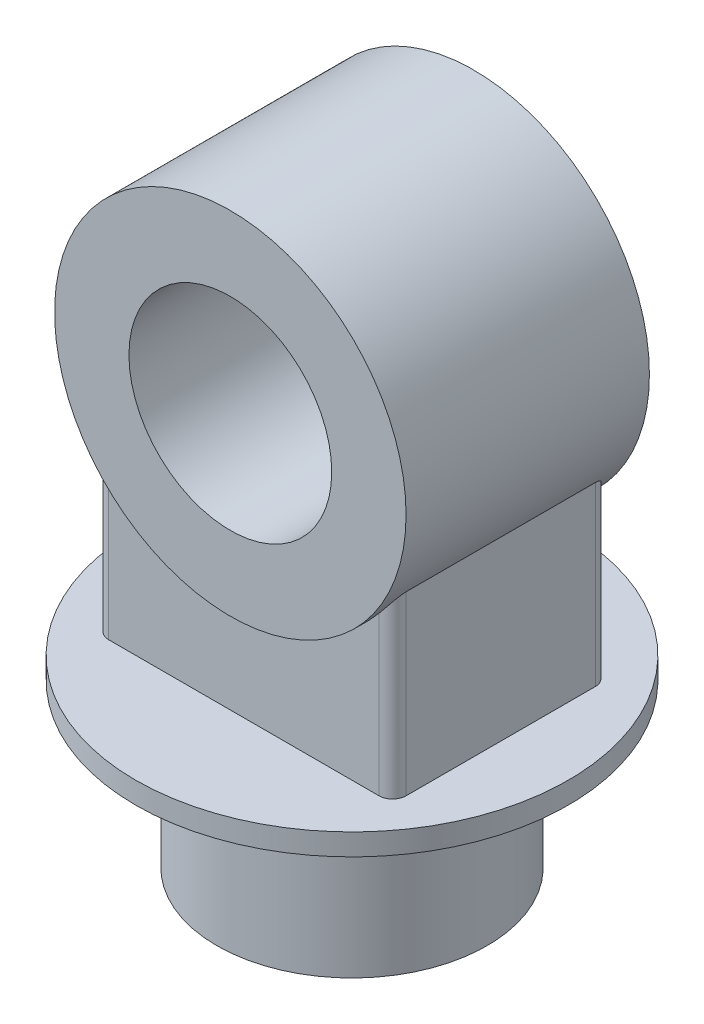
SolidWorks part; units mm, degrees
material "ABS PC"
ref_plane "Front Plane" through (0, 0, 0) normal (0, 0, 1) x (1, 0, 0)
ref_plane "Top Plane" through (0, 0, 0) normal (0, 1, 0) x (1, 0, 0)
ref_plane "Right Plane" through (0, 0, 0) normal (1, 0, 0) x (0, 0, -1)
sketch "Sketch1" plane through (0, 0, 0) normal (0, 1, 0) x (1, 0, 0)
  circle A0 centre (0, 0) radius 100
  dimension "D1" = 200
extrude "Boss-Extrude1" add sketch "Sketch1" along normal blind 120
sketch "Sketch2" plane through (0, 120, 0) normal (0, 1, 0) x (1, 0, 0)
  circle A0 centre (0, 0) radius 160
  dimension "D1" = 320
extrude "Boss-Extrude2" add sketch "Sketch2" along normal blind 16
sketch "Sketch3" plane through (0, 0, 0) normal (0, 0, 1) x (1, 0, 0)
  line L0 (160, 136) -> (-160, 136) construction
  circle A0 centre (0, 336) radius 75
  circle A1 centre (0, 336) radius 130
  dimension "D1" = 150
  dimension "D2" = 260
  dimension "D3" = 200
extrude "Boss-Extrude3" add sketch "Sketch3" along normal mid plane 180 separate body
sketch "Sketch4" plane through (0, 136, 0) normal (0, 1, 0) x (1, 0, 0)
  line L1 (-110, 80) -> (110, 80)
  line L2 (-110, 80) -> (-110, -80)
  line L3 (-110, -80) -> (110, -80)
  line L4 (110, 80) -> (110, -80)
  line L5 (-110, 80) -> (110, -80) construction
  line L6 (-110, -80) -> (110, 80) construction
  point P0 (0, 0)
  dimension "D1" = 160
  dimension "D2" = 220
extrude "Boss-Extrude4" add sketch "Sketch4" along normal up to next
fillet "Fillet1" radius 10 4 edges at (-110, 201.359, 80) (-110, 201.359, -80) (110, 201.359, -80) (110, 201.359, 80)
